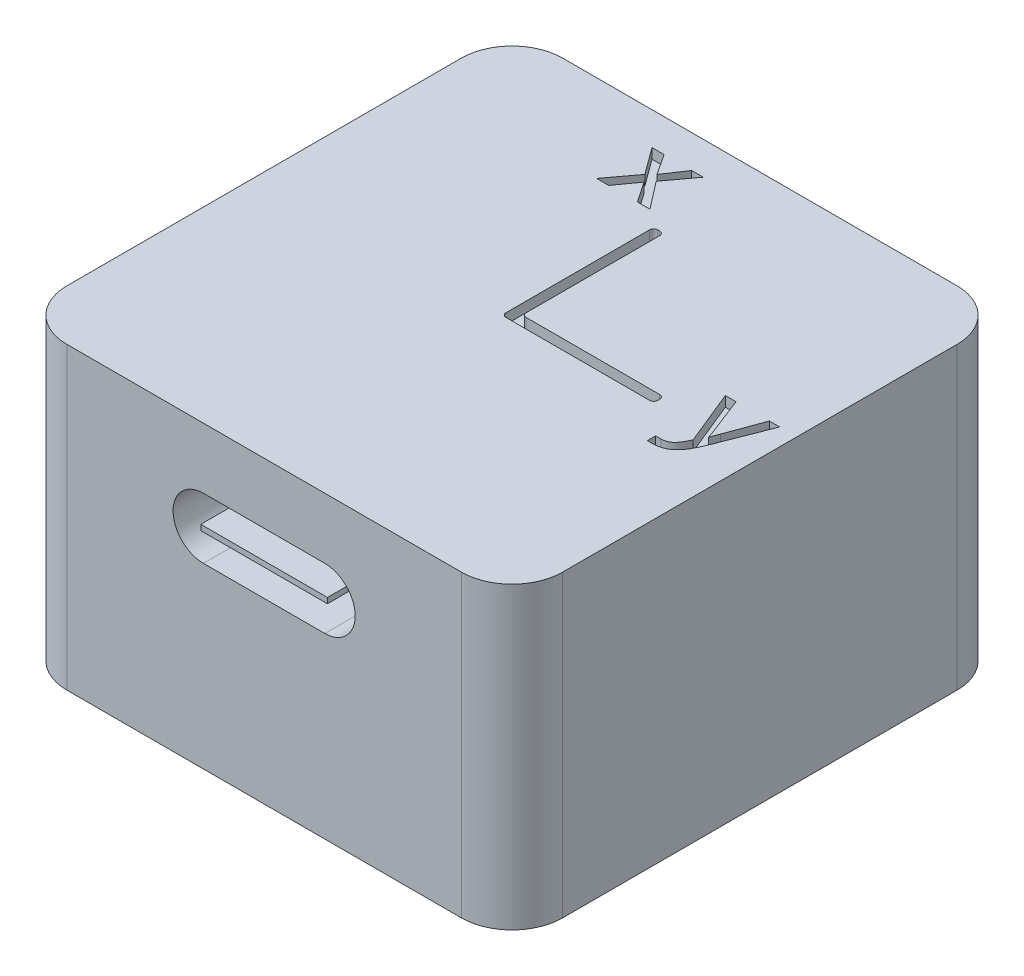
SolidWorks part; units mm, degrees
ref_plane "前视基准面" through (0, 0, 0) normal (0, 0, 1) x (1, 0, 0)
ref_plane "上视基准面" through (0, 0, 0) normal (0, 1, 0) x (1, 0, 0)
ref_plane "右视基准面" through (0, 0, 0) normal (1, 0, 0) x (0, 0, -1)
sketch "草图1" plane through (0, 0, 0) normal (0, 1, 0) x (1, 0, 0)
  line L1 (-9.75, 12.25) -> (9.75, 12.25)
  line L2 (-12.25, 9.75) -> (-12.25, -9.75)
  line L3 (-9.75, -12.25) -> (9.75, -12.25)
  line L4 (12.25, 9.75) -> (12.25, -9.75)
  line L5 (-12.25, 12.25) -> (12.25, -12.25) construction
  line L6 (-12.25, -12.25) -> (12.25, 12.25) construction
  arc A0 (-12.25, -9.75) -> (-9.75, -12.25) centre (-9.75, -9.75) ccw
  arc A1 (9.75, -12.25) -> (12.25, -9.75) centre (9.75, -9.75) ccw
  arc A2 (9.75, 12.25) -> (12.25, 9.75) centre (9.75, 9.75) cw
  arc A3 (-9.75, 12.25) -> (-12.25, 9.75) centre (-9.75, 9.75) ccw
  point P0 (0, 0)
  dimension "D2" = 2.5
  dimension "D1" = 24.5
extrude "凸台-拉伸1" add sketch "草图1" along normal blind 14.8
sketch "草图2" plane through (0, 14.8, 0) normal (0, 1, 0) x (1, 0, 0)
  line L0 (-0.25, -0.05) -> (-0.25, 7.05)
  line L1 (-0.05, 7.25) -> (0.05, 7.25)
  line L2 (0.25, 7.05) -> (0.25, 0.45)
  line L3 (0.45, 0.25) -> (7.05, 0.25)
  line L4 (7.25, 0.05) -> (7.25, -0.05)
  line L5 (7.05, -0.25) -> (-0.05, -0.25)
  line L6 (-0.25, -0.25) -> (0.25, 0.25) construction
  arc A0 (-0.05, -0.25) -> (-0.25, -0.05) centre (-0.05, -0.05) cw
  arc A1 (0.25, 0.45) -> (0.45, 0.25) centre (0.45, 0.45) ccw
  arc A2 (7.25, -0.05) -> (7.05, -0.25) centre (7.05, -0.05) cw
  arc A3 (7.05, 0.25) -> (7.25, 0.05) centre (7.05, 0.05) cw
  arc A4 (0.05, 7.25) -> (0.25, 7.05) centre (0.05, 7.05) cw
  arc A5 (-0.25, 7.05) -> (-0.05, 7.25) centre (-0.05, 7.05) cw
  point P19 (0.25, 7.25)
  point P22 (-0.25, 7.25)
  dimension "D3" = 0.2
  dimension "D1" = 0.5
  dimension "D2" = 7.5
extrude "切除-拉伸1" cut sketch "草图2" against normal blind 0.5
sketch "草图3" plane through (0, 14.8, 0) normal (0, 1, 0) x (1, 0, 0)
  text T0 "x" font "Consolas" height 3.5
extrude "切除-拉伸2" cut sketch "草图3" against normal blind 0.5
sketch "草图4" plane through (0, 14.8, 0) normal (0, 1, 0) x (1, 0, 0)
  text T0 "y" font "Consolas" height 3.5
extrude "切除-拉伸3" cut sketch "草图4" against normal blind 0.5
sketch "草图5" plane through (0, 0, 12.25) normal (0, 0, 1) x (1, 0, 0)
  line L0 (-3, 10.3) -> (3, 10.3) construction
  line L1 (-3, 11.8) -> (3, 11.8)
  line L2 (-3, 8.8) -> (3, 8.8)
  line L3 (0, 10.3) -> (0, 0) construction
  line L4 (-9.75, 0) -> (9.75, 0) construction
  line L5 (-9.75, 14.8) -> (9.75, 14.8) construction
  arc A0 (-3, 11.8) -> (-3, 8.8) centre (-3, 10.3) ccw
  arc A1 (3, 8.8) -> (3, 11.8) centre (3, 10.3) ccw
  point P2 (0, 10.3)
  dimension "D1" = 3
  dimension "D2" = 6
  dimension "D3" = 3
extrude "切除-拉伸4" cut sketch "草图5" against normal blind 5
sketch "草图6" plane through (0, 0, 7.25) normal (0, 0, 1) x (1, 0, 0)
  line L1 (-3.1298, 10.4059) -> (3.1298, 10.4059)
  line L2 (-3.1298, 10.4059) -> (-3.1298, 10.1357)
  line L3 (-3.1298, 10.1357) -> (3.1298, 10.1357)
  line L4 (3.1298, 10.4059) -> (3.1298, 10.1357)
  line L5 (-3.1298, 10.4059) -> (3.1298, 10.1357) construction
  line L6 (-3.1298, 10.1357) -> (3.1298, 10.4059) construction
  point P0 (0, 10.2708)
extrude "凸台-拉伸2" add sketch "草图6" along normal up to surface (5 mm away) up to face at (0, 10.3, 12.25)
